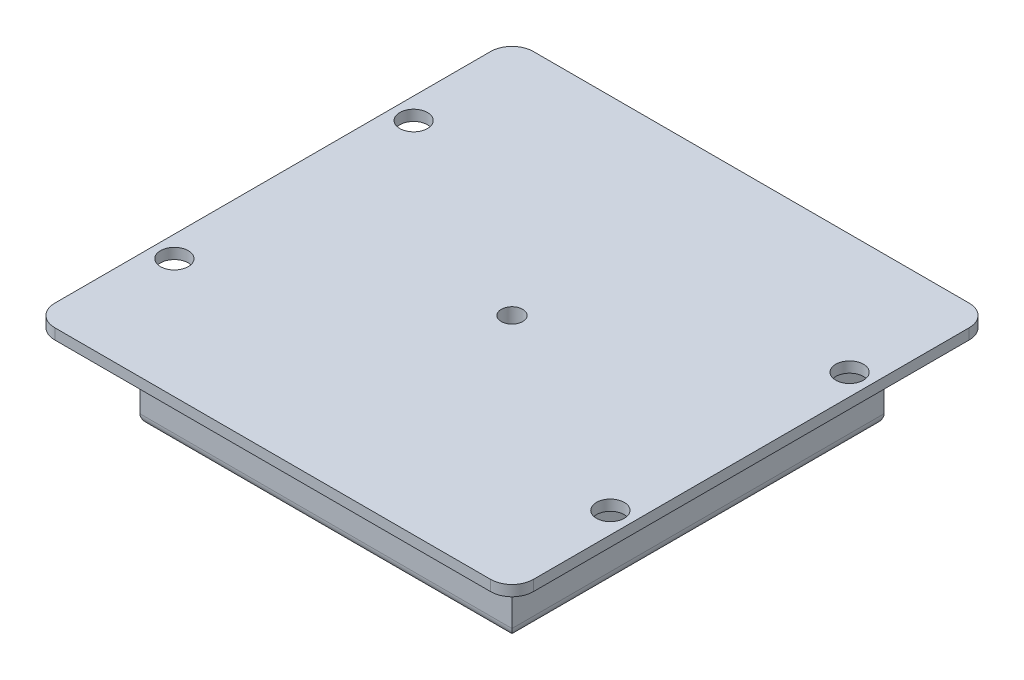
SolidWorks part; units mm, degrees
ref_plane "Front Plane" through (0, 0, 0) normal (0, 0, 1) x (1, 0, 0)
ref_plane "Top Plane" through (0, 0, 0) normal (0, 1, 0) x (1, 0, 0)
ref_plane "Right Plane" through (0, 0, 0) normal (1, 0, 0) x (0, 0, -1)
sketch "Sketch1" plane through (0, 0, 0) normal (0, 1, 0) x (1, 0, 0)
  line L1 (57.15, 57.15) -> (-57.15, 57.15)
  line L2 (57.15, 57.15) -> (57.15, -57.15)
  line L3 (57.15, -57.15) -> (-57.15, -57.15)
  line L4 (-57.15, 57.15) -> (-57.15, -57.15)
  line L5 (57.15, 57.15) -> (-57.15, -57.15) construction
  line L6 (57.15, -57.15) -> (-57.15, 57.15) construction
  point P0 (0, 0)
  dimension "D1" = 114.3
  dimension "D2" = 114.3
extrude "Boss-Extrude1" add sketch "Sketch1" along normal blind 2.54
sketch "Sketch2" plane through (0, 0, 0) normal (0, -1, 0) x (1, 0, 0)
  line L1 (-44.45, 44.45) -> (44.45, 44.45)
  line L2 (-44.45, 44.45) -> (-44.45, -44.45)
  line L3 (-44.45, -44.45) -> (44.45, -44.45)
  line L4 (44.45, 44.45) -> (44.45, -44.45)
  line L5 (-44.45, 44.45) -> (44.45, -44.45) construction
  line L6 (-44.45, -44.45) -> (44.45, 44.45) construction
  point P0 (0, 0)
  dimension "D1" = 88.9
  dimension "D2" = 88.9
extrude "Boss-Extrude2" add sketch "Sketch2" along normal blind 20.32 contours L1 L4 L3 L2
ref_plane "Plane1" through (0, 0, 0) normal (0, 0, 1) x (1, 0, 0)
ref_plane "Plane2" through (0, 0, 0) normal (1, 0, 0) x (0, 0, -1)
hole_wizard "G (0.261) Diameter Hole1" positions "Sketch3" profile "Sketch4" hole size "G" standard "ANSI Inch" end condition through all
sketch "Sketch3" plane through (0, 0, 0) normal (0, -1, 0) x (-1, 0, 0)
  line L0 (-11.176, 0) -> (11.176, 0) construction
  line L1 (0, 11.176) -> (0, -11.176) construction
  point P0 (52.07, -28.575)
  point P6 (52.07, 28.575)
  point P9 (-52.07, -28.575)
  point P10 (-52.07, 28.575)
  dimension "D1" = 57.15
  dimension "D2" = 104.14
sketch "Sketch4" plane through (-52.07, 0, 28.575) normal (1, 0, 0) x (0, 0, -1)
  line L0 (0, 0) -> (0, 2.54)
  line L1 (0, 2.54) -> (3.3147, 2.54)
  line L2 (3.3147, 2.54) -> (3.3147, 0)
  line L5 (3.3147, 0) -> (0, 0)
  line L11 (0, -6.35) -> (0, 107.95) construction
  dimension "Thru Hole Dia." = 6.6294
  dimension "Thru Hole Depth" = 2.54
fillet "Fillet1" radius 2.54 4 edges at (-44.45, -20.32, 0) (0, -20.32, 44.45) (44.45, -20.32, 0) (0, -20.32, -44.45)
fillet "Fillet2" radius 5.08 4 edges at (-57.15, 1.27, -57.15) (-57.15, 1.27, 57.15) (57.15, 1.27, 57.15) (57.15, 1.27, -57.15)
ref_point "Point1"
sketch "Sketch5" plane through (-44.45, 0, 0) normal (-1, 0, 0) x (0, 0, 1)
  line L4 (44.45, 0) -> (-44.45, 0) construction
  line L5 (6.35, -8.89) -> (-6.35, -8.89)
  line L6 (6.35, -8.89) -> (6.35, 0)
  line L7 (6.35, 0) -> (-6.35, 0)
  line L8 (-6.35, -8.89) -> (-6.35, 0)
  circle A0 centre (0, -8.89) radius 6.35
  line M9 (44.45, 0) -> (-44.45, 0)
extrude "Boss-Extrude3" add sketch "Sketch5" along normal blind 12.7 contours L5 A0 | L5 A0 | A0 L6 L8 M9
ref_point "Point2"
sketch "Sketch8" plane through (-57.15, 0, 0) normal (-1, 0, 0) x (0, 0, 1)
  circle A0 centre (0, -8.89) radius 3.81
extrude "Cut-Extrude1" cut sketch "Sketch8" against normal blind 12.7
hole_wizard "1/4-20 Tapped Hole1" positions "Sketch11" profile "Sketch10" tap size "1/4-20" standard "ANSI Inch"
sketch "Sketch11" plane through (0, 2.54, 0) normal (0, 1, 0) x (1, 0, 0)
  point P0 (0, 0)
sketch "Sketch10" plane through (0, 2.54, 0) normal (1, 0, 0) x (0, 0, 1)
  line L0 (0, 0) -> (0, 18.0438)
  line L1 (0, 18.0438) -> (2.5527, 16.51)
  line L2 (2.5527, 16.51) -> (2.5527, 0)
  line L5 (2.5527, 0) -> (0, 0)
  line L10 (0, 18.0438) -> (-2.5527, 16.51) construction
  line L11 (0, -6.35) -> (0, 107.95) construction
  dimension "Tap Drill Dia." = 5.1054
  dimension "Tap Drill Depth" = 16.51
  dimension "Drill Angle" = 118
cosmetic thread "Hole Thread1" parameters "D1"=12.7, "D2"=6.35
